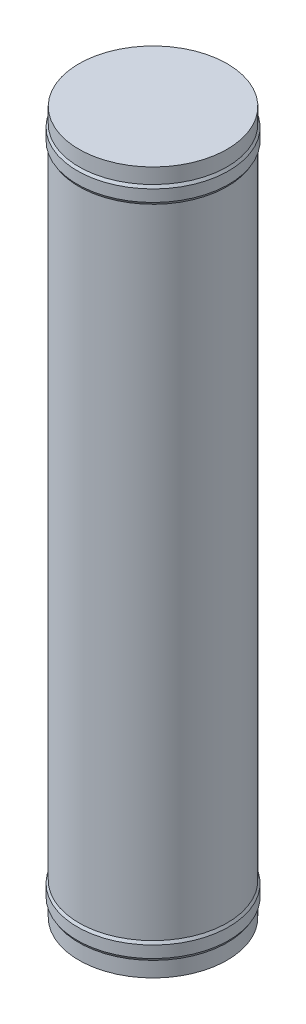
SolidWorks part; units mm, degrees
ref_plane "Front Plane" through (0, 0, 0) normal (0, 0, 1) x (1, 0, 0)
ref_plane "Top Plane" through (0, 0, 0) normal (0, 1, 0) x (1, 0, 0)
ref_plane "Right Plane" through (0, 0, 0) normal (1, 0, 0) x (0, 0, -1)
sketch "Sketch1" plane through (0, 0, 0) normal (0, 0, 1) x (1, 0, 0)
  line L0 (0, 0) -> (9.5, 0) construction
  line L1 (0, -45) -> (0, 45)
  line L2 (0, 45) -> (9.5, 45)
  line L3 (9.5, 45) -> (9.5, 43.05)
  line L4 (9.5, 43.05) -> (9.7, 42.7036)
  line L5 (9.7, 42.7036) -> (9.7, 41.2036)
  line L6 (9.7, 41.2036) -> (9.5, 40.8572)
  line L7 (9.5, 40.8572) -> (9.5, -40.8572)
  line L8 (9.7, -41.2036) -> (9.5, -40.8572)
  line L9 (9.7, -42.7036) -> (9.7, -41.2036)
  line L10 (9.5, -43.05) -> (9.7, -42.7036)
  line L11 (9.5, -45) -> (9.5, -43.05)
  line L12 (0, -45) -> (9.5, -45)
  point P10 (0, 0)
  point P11 (0, 0)
  dimension "D1" = 9.5
  dimension "D2" = 30
  dimension "D3" = 30
  dimension "D4" = 1.5
  dimension "D5" = 0.2
  dimension "D6" = 1.95
  dimension "D7" = 45
revolve "Revolve2" add sketch "Sketch1" angle 360 about L1
